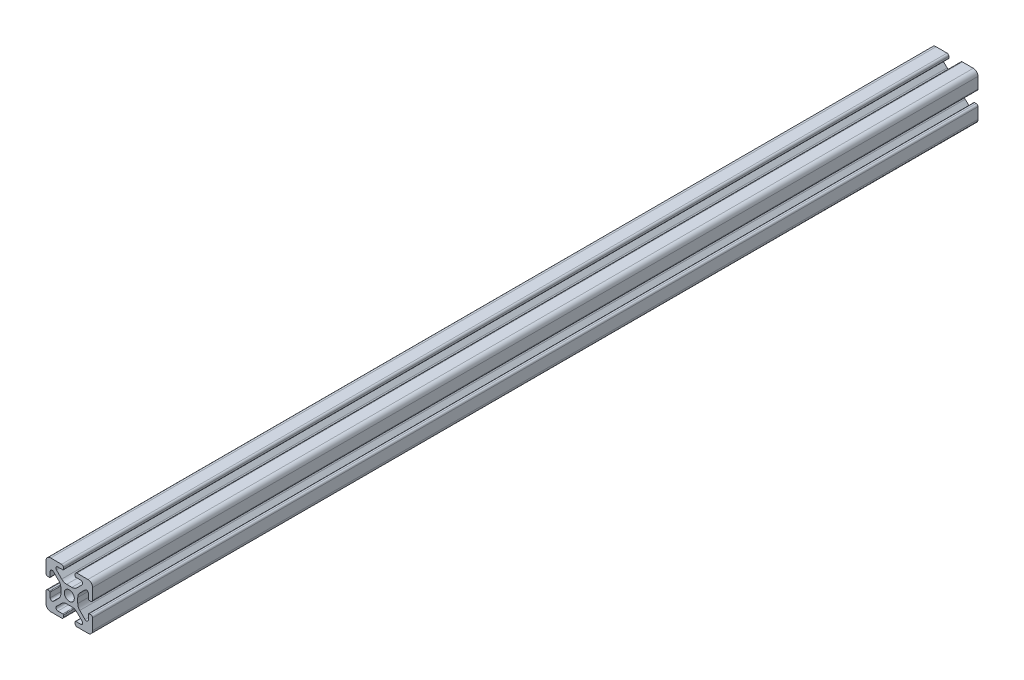
SolidWorks part; units mm, degrees
material "6061-T6 (SS)"
ref_plane "Front Plane" through (0, 0, 0) normal (0, 0, 1) x (1, 0, 0)
ref_plane "Top Plane" through (0, 0, 0) normal (0, 1, 0) x (1, 0, 0)
ref_plane "Right Plane" through (0, 0, 0) normal (1, 0, 0) x (0, 0, -1)
sketch "Sketch1" plane through (0, 0, 0) normal (0, 0, 1) x (1, 0, 0)
  line L2 (-9.9949, 7.9883) -> (-9.9949, 3.2893)
  line L3 (-7.9883, 9.9949) -> (-3.2893, 9.9949)
  line L4 (-2.5019, 9.2075) -> (-2.5019, 8.4963)
  line L5 (-2.8067, 8.1915) -> (-4.9149, 8.1915)
  line L6 (-5.5076, 6.7606) -> (-3.2528, 4.5058)
  line L7 (-6.7606, 5.5076) -> (-4.5058, 3.2528)
  line L8 (-8.1915, 4.9149) -> (-8.1915, 2.8067)
  line L9 (-8.4963, 2.5019) -> (-9.2075, 2.5019)
  line L11 (-1.1334, 3.6279) -> (1.1334, 3.6279)
  line L12 (-3.6279, 1.1334) -> (-3.6279, -1.1334)
  line L13 (8.4963, 2.5019) -> (9.2075, 2.5019)
  line L14 (8.1915, 4.9149) -> (8.1915, 2.8067)
  line L15 (9.9949, 7.9883) -> (9.9949, 3.2893)
  line L16 (7.9883, 9.9949) -> (3.2893, 9.9949)
  line L17 (2.5019, 9.2075) -> (2.5019, 8.4963)
  line L18 (2.8067, 8.1915) -> (4.9149, 8.1915)
  line L19 (3.6279, 1.1334) -> (3.6279, -1.1334)
  line L20 (5.5076, 6.7606) -> (3.2528, 4.5058)
  line L21 (6.7606, 5.5076) -> (4.5058, 3.2528)
  line L22 (-8.4963, -2.5019) -> (-9.2075, -2.5019)
  line L23 (-8.1915, -4.9149) -> (-8.1915, -2.8067)
  line L24 (-6.7606, -5.5076) -> (-4.5058, -3.2528)
  line L25 (-5.5076, -6.7606) -> (-3.2528, -4.5058)
  line L26 (-2.8067, -8.1915) -> (-4.9149, -8.1915)
  line L27 (-2.5019, -9.2075) -> (-2.5019, -8.4963)
  line L28 (-7.9883, -9.9949) -> (-3.2893, -9.9949)
  line L29 (-9.9949, -7.9883) -> (-9.9949, -3.2893)
  line L30 (9.9949, -7.9883) -> (9.9949, -3.2893)
  line L31 (7.9883, -9.9949) -> (3.2893, -9.9949)
  line L32 (2.5019, -9.2075) -> (2.5019, -8.4963)
  line L33 (2.8067, -8.1915) -> (4.9149, -8.1915)
  line L34 (5.5076, -6.7606) -> (3.2528, -4.5058)
  line L35 (6.7606, -5.5076) -> (4.5058, -3.2528)
  line L36 (8.1915, -4.9149) -> (8.1915, -2.8067)
  line L37 (8.4963, -2.5019) -> (9.2075, -2.5019)
  line L38 (-1.1334, -3.6279) -> (1.1334, -3.6279)
  circle A0 centre (0, 0) radius 2.1463
  arc A1 (-9.9949, 7.9883) -> (-7.9883, 9.9949) centre (-7.9883, 7.9883) cw
  arc A2 (-6.7606, 5.5076) -> (-8.1915, 4.9149) centre (-7.3533, 4.9149) ccw
  arc A3 (-4.9149, 8.1915) -> (-5.5076, 6.7606) centre (-4.9149, 7.3533) ccw
  arc A4 (-3.2893, 9.9949) -> (-2.5019, 9.2075) centre (-3.2893, 9.2075) cw
  arc A5 (-9.9949, 3.2893) -> (-9.2075, 2.5019) centre (-9.2075, 3.2893) ccw
  arc A6 (-8.1915, 2.8067) -> (-8.4963, 2.5019) centre (-8.4963, 2.8067) cw
  arc A7 (-2.5019, 8.4963) -> (-2.8067, 8.1915) centre (-2.8067, 8.4963) cw
  arc A8 (-1.1334, 3.6279) -> (-3.2528, 4.5058) centre (-1.1334, 6.6251) cw
  arc A9 (-3.6279, 1.1334) -> (-4.5058, 3.2528) centre (-6.6251, 1.1334) ccw
  arc A10 (8.1915, 2.8067) -> (8.4963, 2.5019) centre (8.4963, 2.8067) ccw
  arc A11 (9.9949, 3.2893) -> (9.2075, 2.5019) centre (9.2075, 3.2893) cw
  arc A12 (9.9949, 7.9883) -> (7.9883, 9.9949) centre (7.9883, 7.9883) ccw
  arc A13 (3.2893, 9.9949) -> (2.5019, 9.2075) centre (3.2893, 9.2075) ccw
  arc A14 (2.5019, 8.4963) -> (2.8067, 8.1915) centre (2.8067, 8.4963) ccw
  arc A15 (1.1334, 3.6279) -> (3.2528, 4.5058) centre (1.1334, 6.6251) ccw
  arc A16 (3.6279, 1.1334) -> (4.5058, 3.2528) centre (6.6251, 1.1334) cw
  arc A17 (6.7606, 5.5076) -> (8.1915, 4.9149) centre (7.3533, 4.9149) cw
  arc A18 (4.9149, 8.1915) -> (5.5076, 6.7606) centre (4.9149, 7.3533) cw
  arc A19 (-3.6279, -1.1334) -> (-4.5058, -3.2528) centre (-6.6251, -1.1334) cw
  arc A20 (-1.1334, -3.6279) -> (-3.2528, -4.5058) centre (-1.1334, -6.6251) ccw
  arc A21 (-2.5019, -8.4963) -> (-2.8067, -8.1915) centre (-2.8067, -8.4963) ccw
  arc A22 (-8.1915, -2.8067) -> (-8.4963, -2.5019) centre (-8.4963, -2.8067) ccw
  arc A23 (-9.9949, -3.2893) -> (-9.2075, -2.5019) centre (-9.2075, -3.2893) cw
  arc A24 (-3.2893, -9.9949) -> (-2.5019, -9.2075) centre (-3.2893, -9.2075) ccw
  arc A25 (-4.9149, -8.1915) -> (-5.5076, -6.7606) centre (-4.9149, -7.3533) cw
  arc A26 (-6.7606, -5.5076) -> (-8.1915, -4.9149) centre (-7.3533, -4.9149) cw
  arc A27 (-9.9949, -7.9883) -> (-7.9883, -9.9949) centre (-7.9883, -7.9883) ccw
  arc A28 (9.9949, -7.9883) -> (7.9883, -9.9949) centre (7.9883, -7.9883) cw
  arc A29 (6.7606, -5.5076) -> (8.1915, -4.9149) centre (7.3533, -4.9149) ccw
  arc A30 (4.9149, -8.1915) -> (5.5076, -6.7606) centre (4.9149, -7.3533) ccw
  arc A31 (3.2893, -9.9949) -> (2.5019, -9.2075) centre (3.2893, -9.2075) cw
  arc A32 (9.9949, -3.2893) -> (9.2075, -2.5019) centre (9.2075, -3.2893) ccw
  arc A33 (8.1915, -2.8067) -> (8.4963, -2.5019) centre (8.4963, -2.8067) cw
  arc A34 (2.5019, -8.4963) -> (2.8067, -8.1915) centre (2.8067, -8.4963) cw
  arc A35 (1.1334, -3.6279) -> (3.2528, -4.5058) centre (1.1334, -6.6251) cw
  arc A36 (3.6279, -1.1334) -> (4.5058, -3.2528) centre (6.6251, -1.1334) ccw
extrude "Boss-Extrude1" add sketch "Sketch1" along normal mid plane 380
